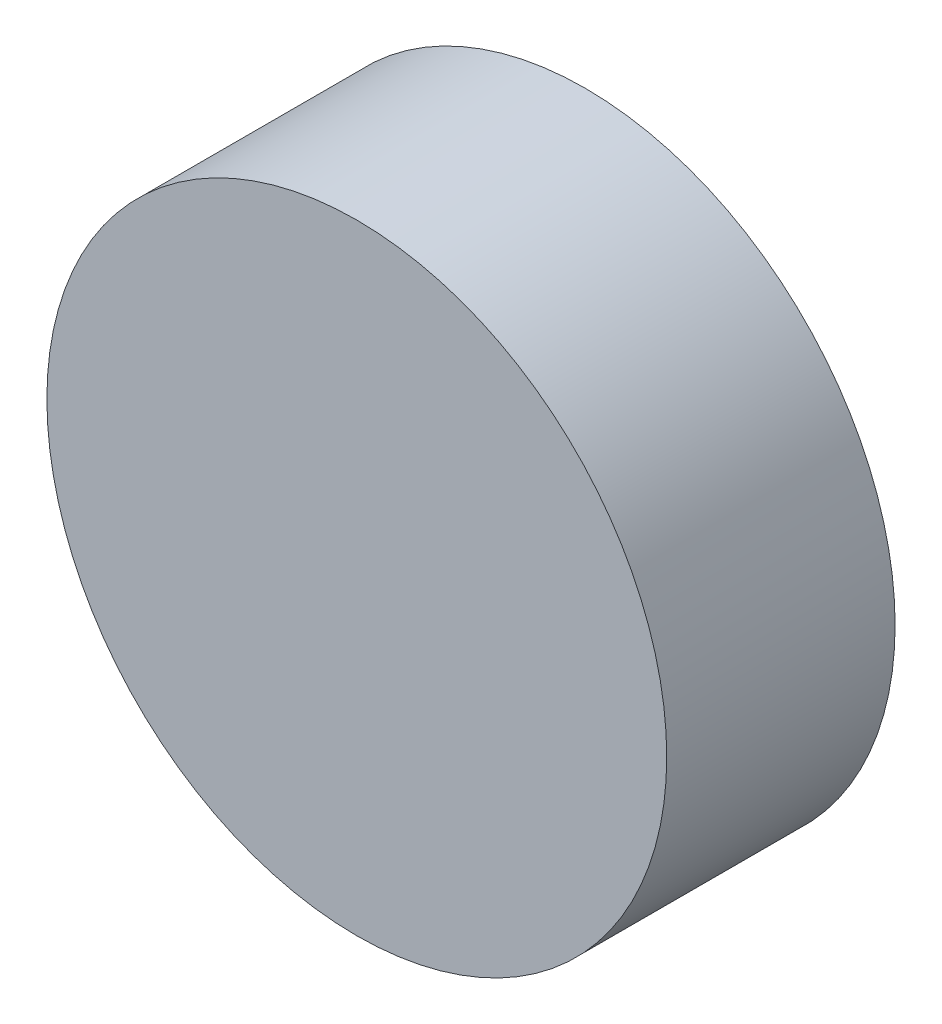
SolidWorks part; units mm, degrees
ref_plane "Front Plane" through (0, 0, 0) normal (0, 0, 1) x (1, 0, 0)
ref_plane "Top Plane" through (0, 0, 0) normal (0, 1, 0) x (1, 0, 0)
ref_plane "Right Plane" through (0, 0, 0) normal (1, 0, 0) x (0, 0, -1)
sketch "Sketch1" plane through (0, 0, 0) normal (0, 0, 1) x (1, 0, 0)
  circle A0 centre (0, 0) radius 19
extrude "Boss-Extrude1" add sketch "Sketch1" along normal blind 14
